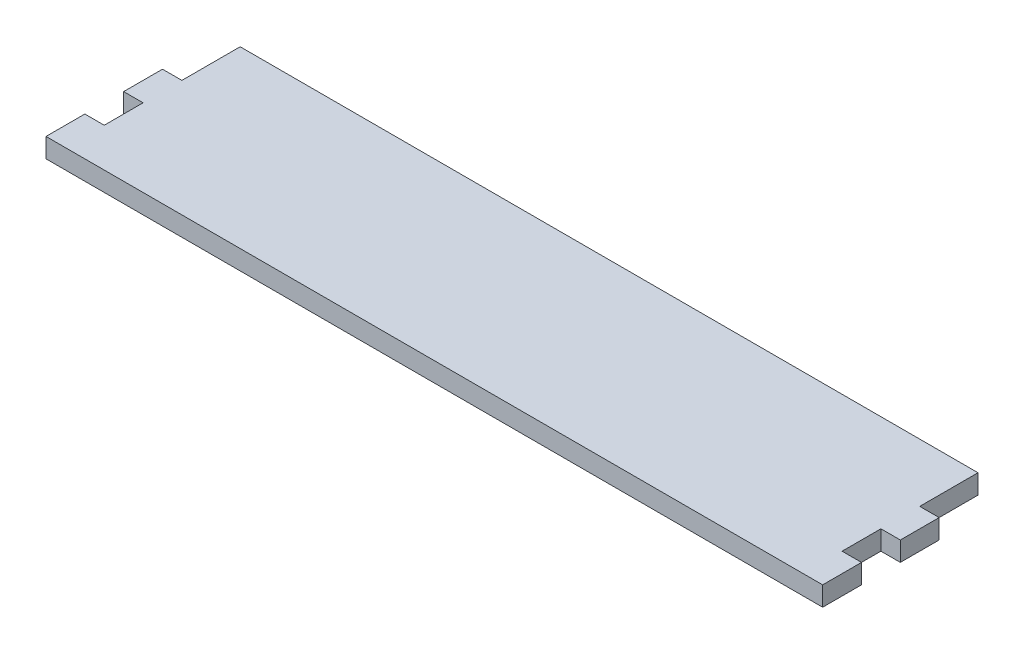
SolidWorks part; units mm, degrees
ref_plane "前视基准面" through (0, 0, 0) normal (0, 0, 1) x (1, 0, 0)
ref_plane "上视基准面" through (0, 0, 0) normal (0, 1, 0) x (1, 0, 0)
ref_plane "右视基准面" through (0, 0, 0) normal (1, 0, 0) x (0, 0, -1)
sketch "草图1" plane through (0, 0, 0) normal (0, 1, 0) x (1, 0, 0)
  line L1 (-100, -22.5) -> (100, -22.5)
  line L2 (-100, -22.5) -> (-100, 22.5)
  line L3 (-100, 22.5) -> (100, 22.5)
  line L4 (100, -22.5) -> (100, 22.5)
  line L5 (-100, -22.5) -> (100, 22.5) construction
  line L6 (-100, 22.5) -> (100, -22.5) construction
  point P0 (0, 0)
  dimension "D1" = 200
  dimension "D2" = 45
extrude "凸台-拉伸1" add sketch "草图1" along normal blind 5
sketch "草图2" plane through (0, 5, 0) normal (0, 1, 0) x (1, 0, 0)
  line L0 (-100, 22.5) -> (-100, -22.5) construction
  line L1 (-100, 22.5) -> (-95, 22.5)
  line L2 (-100, 22.5) -> (-100, 7.5)
  line L3 (-100, 7.5) -> (-95, 7.5)
  line L4 (-95, 22.5) -> (-95, 7.5)
  line L5 (-100, -2.5) -> (-95, -2.5)
  line L6 (-100, -2.5) -> (-100, -12.5)
  line L7 (-100, -12.5) -> (-95, -12.5)
  line L8 (-95, -2.5) -> (-95, -12.5)
  line L9 (100, -22.5) -> (100, 22.5) construction
  line L10 (100, 22.5) -> (95, 22.5)
  line L11 (100, 22.5) -> (100, 7.5)
  line L12 (100, 7.5) -> (95, 7.5)
  line L13 (95, 22.5) -> (95, 7.5)
  line L14 (100, -12.5) -> (95, -12.5)
  line L15 (100, -12.5) -> (100, -2.5)
  line L16 (100, -2.5) -> (95, -2.5)
  line L17 (95, -12.5) -> (95, -2.5)
  line L18 (-100, -22.5) -> (100, -22.5) construction
  dimension "D1" = 5
  dimension "D2" = 10
  dimension "D3" = 15
  dimension "D4" = 10
extrude "切除-拉伸1" cut sketch "草图2" against normal through all
